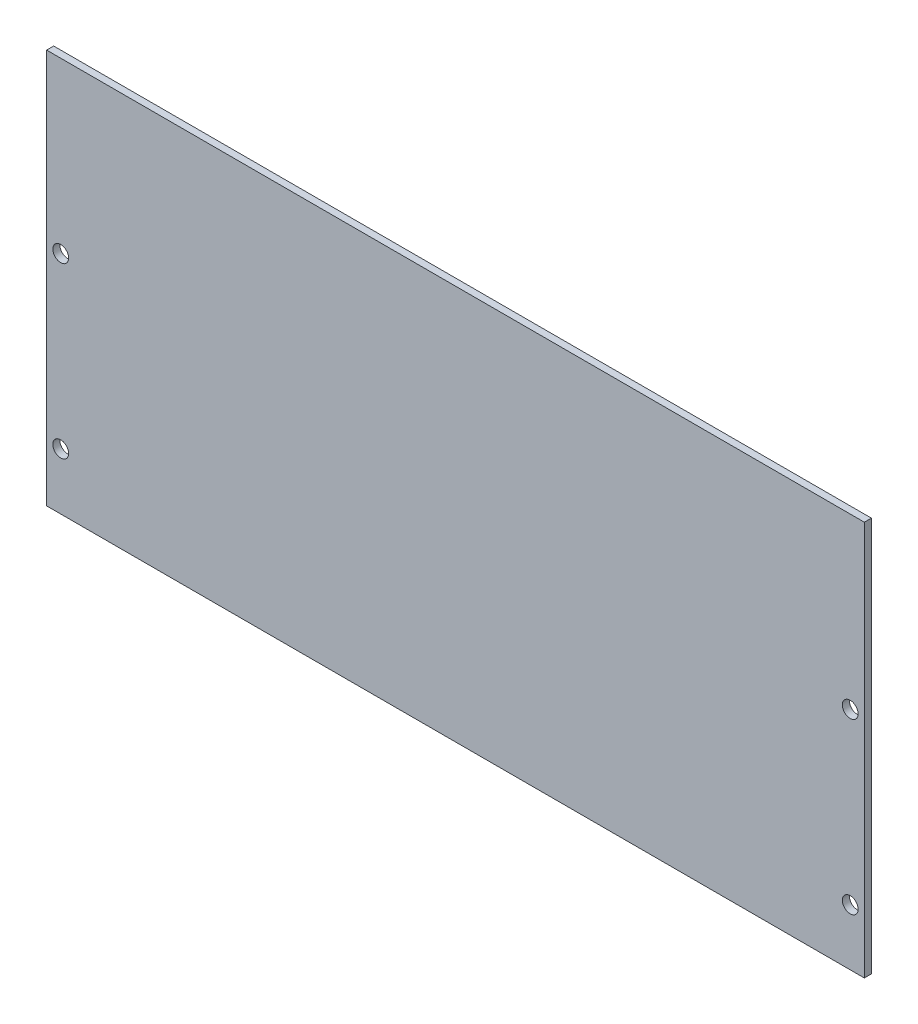
SolidWorks part; units mm, degrees
ref_plane "Front Plane" through (0, 0, 0) normal (0, 0, 1) x (1, 0, 0)
ref_plane "Top Plane" through (0, 0, 0) normal (0, 1, 0) x (1, 0, 0)
ref_plane "Right Plane" through (0, 0, 0) normal (1, 0, 0) x (0, 0, -1)
sketch "Sketch1" plane through (0, 0, 0) normal (0, 0, 1) x (1, 0, 0)
  line L0 (-177.8, 25.4) -> (-177.8, 101.6) construction
  line L1 (-184.15, 177.8) -> (184.15, 177.8)
  line L2 (-184.15, 177.8) -> (-184.15, 0)
  line L3 (-184.15, 0) -> (184.15, 0)
  line L4 (184.15, 177.8) -> (184.15, 0)
  line L5 (0, -55) -> (0, 55) construction
  line L6 (177.8, 25.4) -> (177.8, 101.6) construction
  circle A0 centre (-177.8, 25.4) radius 3.556
  circle A1 centre (-177.8, 101.6) radius 3.556
  circle A2 centre (177.8, 101.6) radius 3.556
  circle A3 centre (177.8, 25.4) radius 3.556
  dimension "D3" = 7.112
  dimension "D4" = 76.2
  dimension "D1" = 368.3
  dimension "D2" = 177.8
  dimension "D5" = 25.4
  dimension "D6" = 6.35
extrude "Boss-Extrude1" add sketch "Sketch1" along normal blind 3.175
